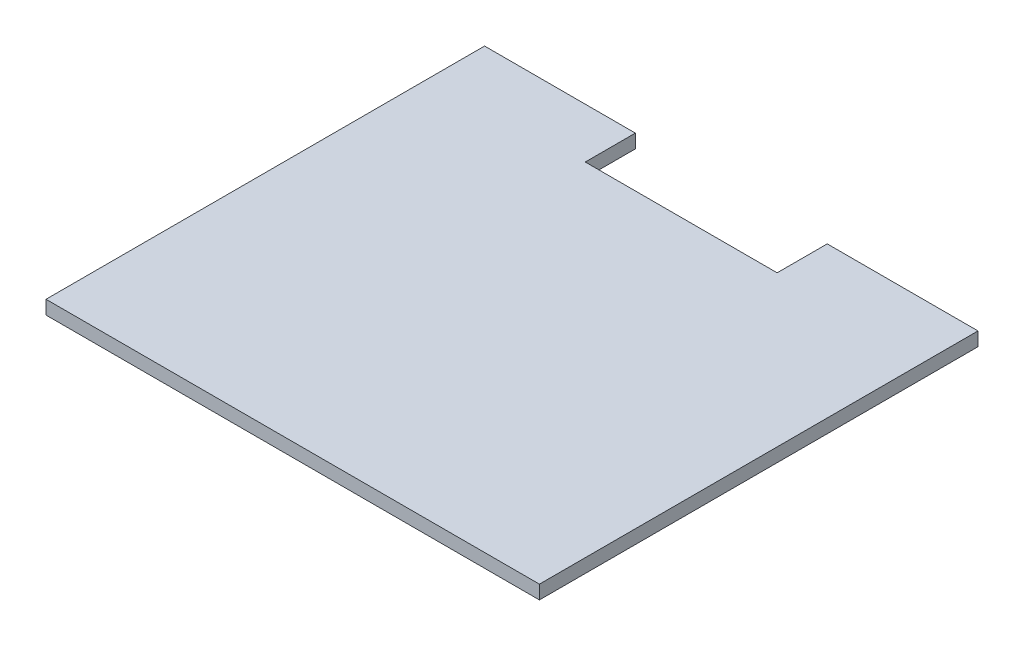
SolidWorks part; units mm, degrees
ref_plane "Front Plane" through (0, 0, 0) normal (0, 0, 1) x (1, 0, 0)
ref_plane "Top Plane" through (0, 0, 0) normal (0, 1, 0) x (1, 0, 0)
ref_plane "Right Plane" through (0, 0, 0) normal (1, 0, 0) x (0, 0, -1)
sketch "Sketch1" plane through (0, 0, 0) normal (0, 1, 0) x (1, 0, 0)
  line L0 (-154.2462, 70.8308) -> (-154.2462, -89.1692)
  line L1 (-154.2462, -89.1692) -> (25.7538, -89.1692)
  line L2 (25.7538, -89.1692) -> (25.7538, 70.8308)
  line L3 (25.7538, 70.8308) -> (-29.2462, 70.8308)
  line L4 (-29.2462, 70.8308) -> (-29.2462, 52.5538)
  line L5 (-29.2462, 52.5538) -> (-99.2462, 52.5538)
  line L6 (-99.2462, 52.5538) -> (-99.2462, 70.8308)
  line L7 (-99.2462, 70.8308) -> (-154.2462, 70.8308)
  dimension "D1" = 180
  dimension "D2" = 160
  dimension "D3" = 160
  dimension "D4" = 55
extrude "Boss-Extrude1" add sketch "Sketch1" along normal blind 5
